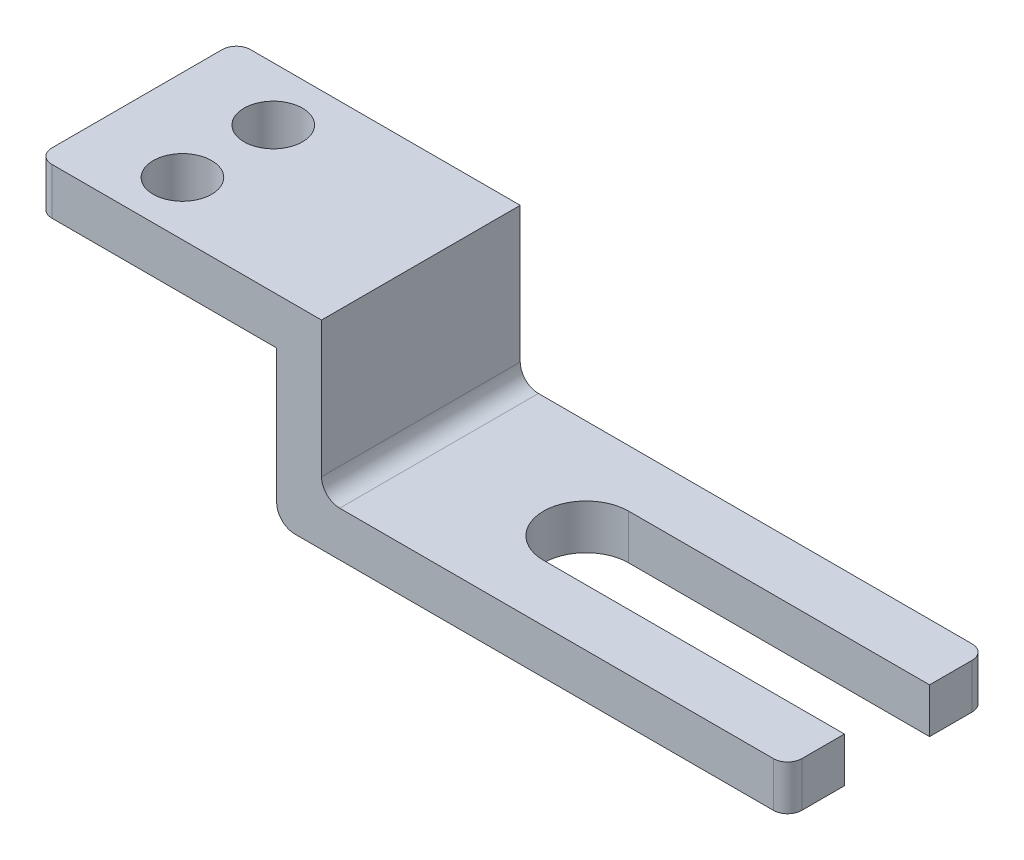
SolidWorks part; units mm, degrees
other "DetailItem1"
material "Ductile Iron"
ref_plane "Frontal" through (0, 0, 0) normal (0, 0, 1) x (1, 0, 0)
ref_plane "Horizontal" through (0, 0, 0) normal (0, 1, 0) x (1, 0, 0)
ref_plane "Profile" through (0, 0, 0) normal (1, 0, 0) x (0, 0, -1)
sketch "Sketch1" plane through (0, 0, 0) normal (0, 0, 1) x (1, 0, 0)
  line L1 (-60.9942, 35.381) -> (6649.6858, 35.381)
  line L2 (-60.9942, 35.381) -> (-60.9942, -1742.619)
  line L3 (-60.9942, -1742.619) -> (6649.6858, -1742.619)
  line L4 (6649.6858, 35.381) -> (6649.6858, -1742.619)
  dimension "D1" = 6710.68
  dimension "D2" = 1778
extrude "Extrude1" add sketch "Sketch1" against normal blind 1778
sketch "Sketch2" plane through (0, 0, 0) normal (0, 0, 1) x (1, 0, 0)
  line L0 (-60.9942, -382.0517) -> (2077.6858, -382.0517)
  line L1 (-60.9942, 35.381) -> (-60.9942, -1742.619) construction
  line L2 (2077.6858, -382.0517) -> (2077.6858, -1758.7317)
  dimension "D1" = 2138.68
  dimension "D2" = 1376.68
extrude "Cut-Extrude3" cut sketch "Sketch2" against normal through all and the other way through all flip side to cut
ref_plane "Plane1" through (-60.9942, 35.381, 0) normal (-1, 0, 0) x (0, 0, 1)
sketch "Sketch6" plane through (0, 0, 0) normal (0, 0, 1) x (1, 0, 0)
  line L0 (2479.0058, 35.381) -> (2479.0058, -1341.299)
  line L1 (6649.6858, 35.381) -> (-60.9942, 35.381) construction
  line L2 (2479.0058, -1341.299) -> (6649.6858, -1341.299)
  line L3 (6649.6858, -1742.619) -> (6649.6858, 35.381) construction
  dimension "D1" = 1376.68
  dimension "D2" = 4170.68
extrude "Cut-Extrude4" cut sketch "Sketch6" against normal through all and the other way through all
sketch "Sketch8" plane through (0, -1341.299, 0) normal (0, 1, 0) x (-1, 0, 0)
  line L0 (-6649.6858, -508) -> (-3957.2858, -508)
  line L1 (-6649.6858, 0) -> (-6649.6858, -1778) construction
  line L3 (-3957.2858, -1270) -> (-6649.6858, -1270)
  arc A0 (-3957.2858, -508) -> (-3957.2858, -1270) centre (-3957.2858, -889) cw
  dimension "D1" = 508
  dimension "D2" = 2692.4
extrude "Cut-Extrude5" cut sketch "Sketch8" against normal through all and the other way through all flip side to cut
sketch "Sketch9" plane through (0, 35.381, 0) normal (0, 1, 0) x (-1, 0, 0)
  line L0 (-2479.0058, 0) -> (-2479.0058, -1778) construction
  line L1 (-2479.0058, 0) -> (60.9942, 0) construction
  circle A0 centre (-751.8058, -1295.4) radius 261.62
  circle A1 centre (-751.8058, -482.6) radius 261.62
  dimension "D3" = 482.6
  dimension "D1" = 1727.2
  dimension "D2" = 812.8
extrude "Cut-Extrude6" cut sketch "Sketch9" against normal through all
fillet "Fillet2" radius 162.56 1 edges at (2479.0058, -1341.299, -889)
fillet "Fillet3" radius 162.56 1 edges at (2077.6858, -1742.619, -889)
fillet "Fillet4" radius 127 4 edges at (6649.6858, -1541.959, -1778) (-60.9942, -173.3354, -1778) (6649.6858, -1541.959, 0) (-60.9942, -173.3354, 0)
